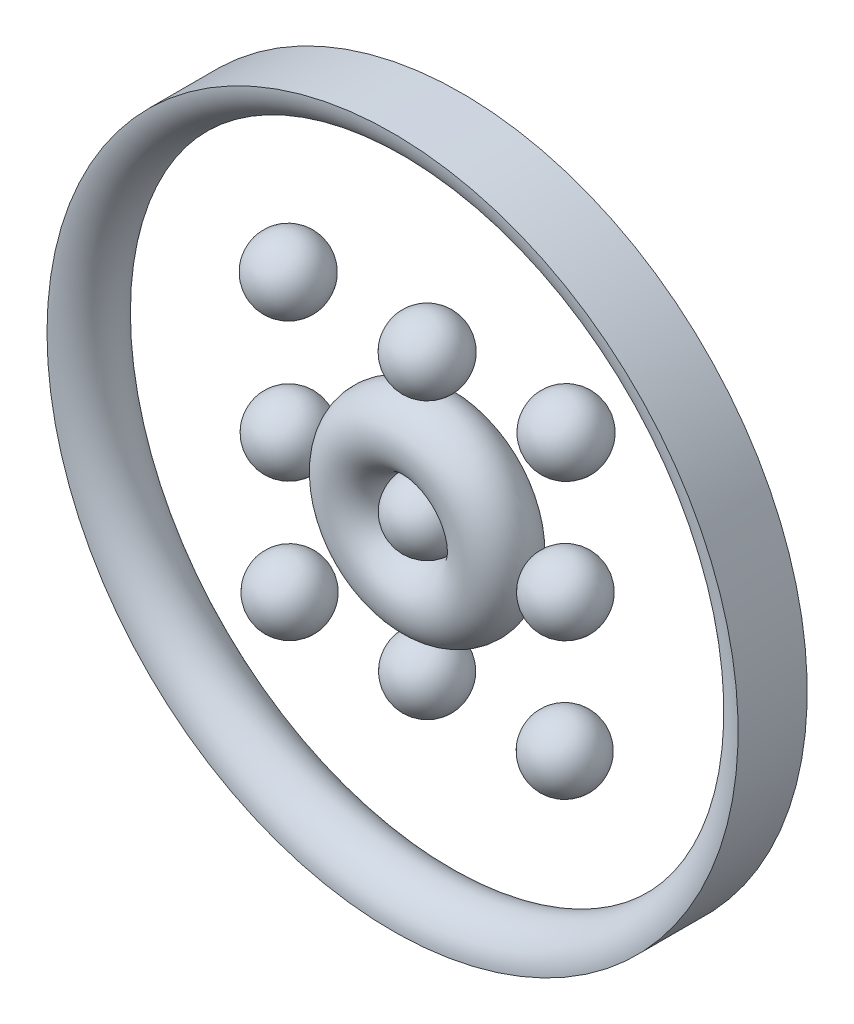
SolidWorks part; units mm, degrees
ref_plane "◯✤ИNⓄᴥ⏀◯✺⦿⚪ꖴ⚪⦿✺◯⏀ᴥⓄИN✤◯" through (0, 0, 0) normal (0, 0, 1) x (1, 0, 0)
ref_plane "◯ߦⓄ✤◯✺⦿⚪ꖴ⚪⦿✺◯✤Ⓞߦ◯" through (0, 0, 0) normal (0, 1, 0) x (1, 0, 0)
ref_plane "◯✤옷ᕤᕦꖴᴥ◯✺⦿⚪ꖴ⚪⦿✺◯ᴥꖴᕤᕦ옷✤◯" through (0, 0, 0) normal (1, 0, 0) x (0, 0, -1)
sketch "◯옷ᑐᑕ✤ᗱᗴ✻ᔓᔕ◯ИNⓄꖴ✤ᑐᑕᗱᗴᔓᔕ◯ᗱᗴᴥᗱᗴ옷ߦᔓᔕ◯✤ИNⓄᴥ⏀◯✺⦿⚪ꖴ⚪⦿✺◯⏀ᴥⓄИN✤◯ᔓᔕߦ옷ᗱᗴᴥᗱᗴ◯ᔓᔕᗱᗴᑐᑕ✤ꖴⓄИN◯ᔓᔕ✻ᗱᗴ✤ᑐᑕ옷◯" plane through (0, 0, 0) normal (0, 0, 1) x (1, 0, 0)
  line L0 (0, 0) -> (0, 0.5) construction
  line L1 (0, 0) -> (0.3536, 0.3536) construction
  line L2 (0, 0) -> (0.5, 0) construction
  line L3 (0, 0) -> (0.3536, -0.3536) construction
  line L4 (0, 0) -> (0, -0.5) construction
  line L5 (0, 0) -> (-0.3536, -0.3536) construction
  line L6 (0, 0) -> (-0.5, 0) construction
  line L7 (0, 0) -> (-0.3536, 0.3536) construction
  circle A0 centre (0, 0) radius 0.5 construction
  point P13 (0, 0)
  dimension "D1" = 8
sketch "◯옷ᑐᑕ✤ᗱᗴ✻ᔓᔕ◯ИNⓄꖴ✤ᑐᑕᗱᗴᔓᔕ◯ᗱᗴᴥᗱᗴ옷ߦᔓᔕ◯✤옷ᕤᕦꖴᴥ◯✺⦿⚪ꖴ⚪⦿✺◯ᴥꖴᕤᕦ옷✤◯ᔓᔕߦ옷ᗱᗴᴥᗱᗴ◯ᔓᔕᗱᗴᑐᑕ✤ꖴⓄИN◯ᔓᔕ✻ᗱᗴ✤ᑐᑕ옷◯" plane through (0, 0, 0) normal (1, 0, 0) x (0, 0, -1)
  line L0 (0, -0.5) -> (0, 0.5) construction
  line L1 (0, 0) -> (-0.5, 0) construction
  line L2 (-0.3536, 0.3536) -> (0, 0) construction
  line L3 (-0.3536, -0.3536) -> (0, 0) construction
  arc A0 (0, 0.5) -> (-0.5, 0) centre (0, 0) ccw construction
  arc A1 (0, -0.5) -> (-0.5, 0) centre (0, 0) cw construction
sketch "◯옷ᑐᑕ✤ᗱᗴ✻ᔓᔕ◯ИNⓄꖴ✤ᑐᑕᗱᗴᔓᔕ◯ᗱᗴᴥᗱᗴ옷ߦᔓᔕ◯ߦⓄ✤◯✺⦿⚪ꖴ⚪⦿✺◯✤Ⓞߦ◯ᔓᔕߦ옷ᗱᗴᴥᗱᗴ◯ᔓᔕᗱᗴᑐᑕ✤ꖴⓄИN◯ᔓᔕ✻ᗱᗴ✤ᑐᑕ옷◯" plane through (0, 0, 0) normal (0, 1, 0) x (1, 0, 0)
  line L0 (0.5, 0) -> (-0.5, 0) construction
  line L1 (0, 0) -> (0, -0.5) construction
  line L2 (-0.3536, -0.3536) -> (0, 0) construction
  line L3 (0.3536, -0.3536) -> (0, 0) construction
  arc A0 (-0.5, 0) -> (0, -0.5) centre (0, 0) ccw construction
  arc A1 (0.5, 0) -> (0, -0.5) centre (0, 0) cw construction
ref_plane "◯✤옷ᕤᕦꖴᴥ◯ߦⓄ✤◯✺⦿⚪ꖴ⚪⦿✺◯✤Ⓞߦ◯ᴥꖴᕤᕦ옷✤◯" through (0, 0, 0) normal (-0.7071, 0.7071, 0) x (0.7071, 0.7071, 0)
ref_plane "◯✤⏀ᗱᗴᙁ◯ߦⓄ✤◯✺⦿⚪ꖴ⚪⦿✺◯✤Ⓞߦ◯ᙁᗱᗴ⏀✤◯" through (0, 0, 0) normal (0.7071, 0.7071, 0) x (0.7071, -0.7071, 0)
ref_plane "◯·◯ߦⓄ✤◯✤ИNⓄᴥ⏀◯✺⦿⚪ꖴ⚪⦿✺◯⏀ᴥⓄИN✤◯✤Ⓞߦ◯·◯" through (0, 0, 0) normal (0, 0.7071, 0.7071) x (1, 0, 0)
ref_plane "◯✤옷ᕤᕦꖴᴥ◯✤ИNⓄᴥ⏀◯✺⦿⚪ꖴ⚪⦿✺◯⏀ᴥⓄИN✤◯ᴥꖴᕤᕦ옷✤◯" through (0, 0, 0) normal (0.7071, 0, 0.7071) x (0.7071, 0, -0.7071)
ref_plane "◯ߦⓄ✤◯✤ИNⓄᴥ⏀◯✺⦿⚪ꖴ⚪⦿✺◯⏀ᴥⓄИN✤◯✤Ⓞߦ◯" through (0, 0, 0) normal (0, -0.7071, 0.7071) x (1, 0, 0)
ref_plane "◯·◯✤옷ᕤᕦꖴᴥ◯✤ИNⓄᴥ⏀◯✺⦿⚪ꖴ⚪⦿✺◯⏀ᴥⓄИN✤◯ᴥꖴᕤᕦ옷✤◯·◯" through (0, 0, 0) normal (-0.7071, 0, 0.7071) x (0.7071, 0, 0.7071)
sketch "◯옷ᑐᑕ✤ᗱᗴ✻ᔓᔕ◯ИNⓄꖴ✤ᑐᑕᗱᗴᔓᔕ◯ᗱᗴᴥᗱᗴ옷ߦᔓᔕ◯·◯ߦⓄ✤◯✤ИNⓄᴥ⏀◯✺⦿⚪ꖴ⚪⦿✺◯⏀ᴥⓄИN✤◯✤Ⓞߦ◯·◯ᔓᔕߦ옷ᗱᗴᴥᗱᗴ◯ᔓᔕᗱᗴᑐᑕ✤ꖴⓄИN◯ᔓᔕ✻ᗱᗴ✤ᑐᑕ옷◯" plane through (0, 0, 0) normal (0, 0.7071, 0.7071) x (1, 0, 0)
  line L0 (-0.2887, -0.4082) -> (0, 0) construction
  line L1 (0.2887, -0.4082) -> (0, 0) construction
  arc A0 (-0.2887, -0.4082) -> (0.2887, -0.4082) centre (0, 0) ccw construction
sketch "◯옷ᑐᑕ✤ᗱᗴ✻ᔓᔕ◯ИNⓄꖴ✤ᑐᑕᗱᗴᔓᔕ◯ᗱᗴᴥᗱᗴ옷ߦᔓᔕ◯✤옷ᕤᕦꖴᴥ◯✤ИNⓄᴥ⏀◯✺⦿⚪ꖴ⚪⦿✺◯⏀ᴥⓄИN✤◯ᴥꖴᕤᕦ옷✤◯ᔓᔕߦ옷ᗱᗴᴥᗱᗴ◯ᔓᔕᗱᗴᑐᑕ✤ꖴⓄИN◯ᔓᔕ✻ᗱᗴ✤ᑐᑕ옷◯" plane through (0, 0, 0) normal (0.7071, 0, 0.7071) x (0.7071, 0, -0.7071)
  line L0 (-0.4082, -0.2887) -> (0, 0) construction
  line L1 (-0.4082, -0.2887) -> (0, 0) construction
  line L2 (-0.4082, 0.2887) -> (0, 0) construction
  arc A0 (-0.4082, 0.2887) -> (-0.4082, -0.2887) centre (0, 0) ccw construction
sketch "◯옷ᑐᑕ✤ᗱᗴ✻ᔓᔕ◯ИNⓄꖴ✤ᑐᑕᗱᗴᔓᔕ◯ᗱᗴᴥᗱᗴ옷ߦᔓᔕ◯ߦⓄ✤◯✤ИNⓄᴥ⏀◯✺⦿⚪ꖴ⚪⦿✺◯⏀ᴥⓄИN✤◯✤Ⓞߦ◯ᔓᔕߦ옷ᗱᗴᴥᗱᗴ◯ᔓᔕᗱᗴᑐᑕ✤ꖴⓄИN◯ᔓᔕ✻ᗱᗴ✤ᑐᑕ옷◯" plane through (0, 0, 0) normal (0, -0.7071, 0.7071) x (1, 0, 0)
  line L0 (-0.2887, 0.4082) -> (0, 0) construction
  line L1 (-0.2887, 0.4082) -> (0, 0) construction
  line L2 (0.2887, 0.4082) -> (0, 0) construction
  arc A0 (0.2887, 0.4082) -> (-0.2887, 0.4082) centre (0, 0) ccw construction
sketch "◯옷ᑐᑕ✤ᗱᗴ✻ᔓᔕ◯ИNⓄꖴ✤ᑐᑕᗱᗴᔓᔕ◯ᗱᗴᴥᗱᗴ옷ߦᔓᔕ◯·◯✤옷ᕤᕦꖴᴥ◯✤ИNⓄᴥ⏀◯✺⦿⚪ꖴ⚪⦿✺◯⏀ᴥⓄИN✤◯ᴥꖴᕤᕦ옷✤◯·◯ᔓᔕߦ옷ᗱᗴᴥᗱᗴ◯ᔓᔕᗱᗴᑐᑕ✤ꖴⓄИN◯ᔓᔕ✻ᗱᗴ✤ᑐᑕ옷◯" plane through (0, 0, 0) normal (-0.7071, 0, 0.7071) x (0.7071, 0, 0.7071)
  line L0 (0.4082, 0.2887) -> (0, 0) construction
  line L1 (0.4082, -0.2887) -> (0, 0) construction
  line L2 (0.4082, 0.2887) -> (0, 0) construction
  line L3 (0.4082, -0.2887) -> (0, 0) construction
  arc A0 (0.4082, -0.2887) -> (0.4082, 0.2887) centre (0, 0) ccw construction
other "Freeze***"
sketch "Sketch15" plane through (0, 0, 0) normal (0, 0, 1) x (1, 0, 0)
  line L0 (0, 0) -> (-276.1109, 24998.4752)
  line L1 (0, 0) -> (-245.433, 24998.7952)
  line L2 (0, 0) -> (-306.7885, 24998.1175)
  line L3 (0, 0) -> (-214.7547, 24999.0776)
  line L4 (0, 0) -> (-184.076, 24999.3223)
  line L5 (0, 0) -> (-153.3971, 24999.5294)
  line L6 (0, 0) -> (-122.718, 24999.6988)
  line L7 (0, 0) -> (-92.0386, 24999.8306)
  line L8 (0, 0) -> (-61.3592, 24999.9247)
  line L9 (0, 0) -> (-30.6796, 24999.9812)
  line L10 (0, 0) -> (0, 25000)
  line L11 (0, 0) -> (30.6796, 24999.9812)
  line L12 (0, 0) -> (61.3592, 24999.9247)
  line L13 (0, 0) -> (92.0386, 24999.8306)
  line L14 (0, 0) -> (122.718, 24999.6988)
  line L15 (0, 0) -> (153.3971, 24999.5294)
  line L16 (0, 0) -> (184.076, 24999.3223)
  line L17 (0, 0) -> (214.7547, 24999.0776)
  line L18 (0, 0) -> (245.433, 24998.7952)
  line L19 (0, 0) -> (276.1109, 24998.4752)
  line L20 (0, 0) -> (306.7885, 24998.1175)
  circle A0 centre (0, 0) radius 25000
  circle A1 centre (0, 24696.9307) radius 303.0693
  circle A10 centre (0, 24696.9307) radius 30.3077
  circle A12 centre (-60.6153, 24696.8563) radius 30.3077 construction
  circle A13 centre (-121.2303, 24696.6331) radius 30.3077
  circle A20 centre (0, 24696.9307) radius 151.5383 construction
  circle A22 centre (0, 24757.6205) radius 30.3822 construction
  circle A33 centre (0, 24098.1401) radius 295.7212
  circle A34 centre (0, 24818.4595) radius 30.4568
  circle A35 centre (0, 24636.3896) radius 30.2334 construction
  circle A36 centre (0, 24575.9969) radius 30.1593
  circle A38 centre (-60.9136, 24818.3848) radius 30.4568 construction
  circle A39 centre (-60.7643, 24757.546) radius 30.3822 construction
  circle A40 centre (-60.4667, 24636.3154) radius 30.2334 construction
  circle A41 centre (-60.3185, 24575.9229) radius 30.1593 construction
  circle A42 centre (-120.6367, 24575.7008) radius 30.1593
  circle A43 centre (-120.9331, 24636.0928) radius 30.2334 construction
  circle A44 centre (-121.2303, 24696.6331) radius 30.3077
  circle A45 centre (-121.5282, 24757.3222) radius 30.3822 construction
  circle A46 centre (-121.8268, 24818.1605) radius 30.4568
  circle A47 centre (60.9136, 24818.3848) radius 30.4568 construction
  circle A48 centre (60.7643, 24757.546) radius 30.3822 construction
  circle A49 centre (60.6153, 24696.8563) radius 30.3077 construction
  circle A50 centre (60.4667, 24636.3154) radius 30.2334 construction
  circle A51 centre (60.3185, 24575.9229) radius 30.1593 construction
  circle A52 centre (120.6367, 24575.7008) radius 30.1593
  circle A53 centre (120.9331, 24636.0928) radius 30.2334 construction
  circle A54 centre (121.2303, 24696.6331) radius 30.3077
  circle A55 centre (121.5282, 24757.3222) radius 30.3822 construction
  circle A56 centre (121.8268, 24818.1605) radius 30.4568
  circle A57 centre (0, 24696.9307) radius 90.923 construction
  circle A58 centre (0, 24696.9307) radius 272.7637
  point P28 (0, 0)
  point P42 (0, 0)
  point P49 (0, 0)
  dimension "D1" = 21
sketch "Sketch16" plane through (0, 0, 0) normal (0, 0, 1) x (1, 0, 0)
  line L0 (30.3077, 24696.9307) -> (-30.3077, 24696.9307)
  circle A0 centre (0, 24696.9307) radius 30.3077 construction
  arc A1 (30.3077, 24696.9307) -> (-30.3077, 24696.9307) centre (0, 24696.9307) ccw
revolve "Revolve12" add sketch "Sketch16" angle 360 about L0
sketch "Sketch17" plane through (0, 0, 0) normal (0, 0, 1) x (1, 0, 0)
  line L0 (30.1593, 24575.9969) -> (-30.1593, 24575.9969)
  circle A0 centre (0, 24575.9969) radius 30.1593 construction
  arc A1 (30.1593, 24575.9969) -> (-30.1593, 24575.9969) centre (0, 24575.9969) ccw
revolve "Revolve13" add sketch "Sketch17" angle 360 about L0
sketch "Sketch18" plane through (0, 0, 0) normal (0, 0, 1) x (1, 0, 0)
  line L0 (30.4568, 24818.4595) -> (-30.4568, 24818.4595)
  circle A0 centre (0, 24818.4595) radius 30.4568 construction
  arc A1 (30.4568, 24818.4595) -> (-30.4568, 24818.4595) centre (0, 24818.4595) ccw
revolve "Revolve14" add sketch "Sketch18" angle 360 about L0
sketch "Sketch19" plane through (0, 0, 0) normal (0, 0, 1) x (1, 0, 0)
  line L0 (150.7959, 24575.7008) -> (90.4774, 24575.7008)
  circle A0 centre (120.6367, 24575.7008) radius 30.1593 construction
  arc A1 (150.7959, 24575.7008) -> (90.4774, 24575.7008) centre (120.6367, 24575.7008) ccw
revolve "Revolve15" add sketch "Sketch19" angle 360 about L0
sketch "Sketch20" plane through (0, 0, 0) normal (0, 0, 1) x (1, 0, 0)
  line L0 (-90.4774, 24575.7008) -> (-150.7959, 24575.7008)
  circle A0 centre (-120.6367, 24575.7008) radius 30.1593 construction
  arc A1 (-90.4774, 24575.7008) -> (-150.7959, 24575.7008) centre (-120.6367, 24575.7008) ccw
revolve "Revolve16" add sketch "Sketch20" angle 360 about L0
sketch "Sketch21" plane through (0, 0, 0) normal (0, 0, 1) x (1, 0, 0)
  line L0 (151.538, 24696.6331) -> (90.9226, 24696.6331)
  circle A0 centre (121.2303, 24696.6331) radius 30.3077 construction
  arc A1 (151.538, 24696.6331) -> (90.9226, 24696.6331) centre (121.2303, 24696.6331) ccw
revolve "Revolve17" add sketch "Sketch21" angle 360 about L0
sketch "Sketch22" plane through (0, 0, 0) normal (0, 0, 1) x (1, 0, 0)
  line L0 (-90.9226, 24696.6331) -> (-151.538, 24696.6331)
  circle A0 centre (-121.2303, 24696.6331) radius 30.3077 construction
  arc A1 (-90.9226, 24696.6331) -> (-151.538, 24696.6331) centre (-121.2303, 24696.6331) ccw
revolve "Revolve18" add sketch "Sketch22" angle 360 about L0
sketch "Sketch23" plane through (0, 0, 0) normal (0, 0, 1) x (1, 0, 0)
  line L0 (152.2837, 24818.1605) -> (91.37, 24818.1605)
  circle A0 centre (121.8268, 24818.1605) radius 30.4568 construction
  arc A1 (152.2837, 24818.1605) -> (91.37, 24818.1605) centre (121.8268, 24818.1605) ccw
revolve "Revolve19" add sketch "Sketch23" angle 360 about L0
sketch "Sketch24" plane through (0, 0, 0) normal (0, 0, 1) x (1, 0, 0)
  line L2 (-91.37, 24818.1605) -> (-152.2837, 24818.1605)
  circle A2 centre (-121.8268, 24818.1605) radius 30.4568 construction
  arc A3 (-91.37, 24818.1605) -> (-152.2837, 24818.1605) centre (-121.8268, 24818.1605) ccw
revolve "Revolve20" add sketch "Sketch24" angle 360 about L2
sketch "Sketch25" plane through (0, 0, 0) normal (1, 0, 0) x (0, 0, -1)
  line L1 (0, 24696.9307) -> (-84.406, 24696.9307) construction
  line L3 (0, 24666.623) -> (0, 24606.1562) construction
  circle A2 centre (0, 24636.3896) radius 30.2334
revolve "Revolve21" add sketch "Sketch25" angle 360 about L1
sketch "Sketch26" plane through (0, 0, 0) normal (1, 0, 0) x (0, 0, -1)
  line L0 (0, 24969.6944) -> (0, 24424.167) construction
  line L2 (0, 24696.9307) -> (-84.406, 24696.9307) construction
  line L3 (30.3056, 25000) -> (-30.3056, 25000)
  arc A0 (-30.3056, 25000) -> (30.3056, 25000) centre (0, 25000) ccw
revolve "Revolve22" add sketch "Sketch26" angle 360 about L2
sketch "Sketch27" plane through (0, 0, 0) normal (0, 0, 1) x (1, 0, 0)
  line L0 (0, 24696.9307) -> (0, 24455.6554)
  line L1 (0, 24969.6944) -> (0, 25000)
  line L2 (-30.6796, 24999.9812) -> (30.6796, 24999.9812)
  circle A0 centre (0, 24696.9307) radius 30.3077 construction
  circle A1 centre (0, 24696.9307) radius 30.3077
  circle A2 centre (-121.2303, 24696.6331) radius 30.3077 construction
  circle A4 centre (-121.2303, 24696.6331) radius 30.3077
  circle A6 centre (0, 24818.4595) radius 30.4568 construction
  circle A7 centre (0, 24818.4595) radius 30.4568
  circle A8 centre (0, 24575.9969) radius 30.1593 construction
  circle A9 centre (0, 24575.9969) radius 30.1593
  circle A10 centre (120.6367, 24575.7008) radius 30.1593 construction
  circle A11 centre (0, 24636.3896) radius 30.2334 construction
  circle A12 centre (0, 24636.3896) radius 30.2334
  circle A13 centre (120.6367, 24575.7008) radius 30.1593
  circle A14 centre (121.8268, 24818.1605) radius 30.4568 construction
  circle A15 centre (121.8268, 24818.1605) radius 30.4568
  circle A16 centre (0, 24696.9307) radius 272.7637 construction
  circle A17 centre (0, 24696.9307) radius 272.7637
  circle A18 centre (0, 24696.9307) radius 303.0693 construction
  circle A19 centre (0, 24696.9307) radius 303.0693
  arc A20 (-30.3056, 24999.9812) -> (30.3056, 24999.9812) centre (0, 25000) ccw
  circle A21 centre (0, 24098.1401) radius 295.7212 construction
  circle A22 centre (0, 24098.1401) radius 295.7212
  circle A23 centre (0, 24515.7523) radius 30.0853 construction
  circle A24 centre (0, 24455.6554) radius 30.0116 construction
  circle A25 centre (0, 24455.6554) radius 10.0039 construction
  point P0 (0, 0)
sketch "Sketch29" plane through (0, 0, 0) normal (1, 0, 0) x (0, 0, -1)
  line L0 (0, 24666.623) -> (0, 24606.1562) construction
  line L1 (0, 24666.623) -> (0, 24606.1562)
  line L2 (0, 24485.667) -> (0, 24425.6438) construction
  line L3 (0, 24485.667) -> (0, 24425.6438)
  circle A0 centre (0, 24636.3896) radius 30.2334
  circle A1 centre (0, 24455.6554) radius 30.0116
